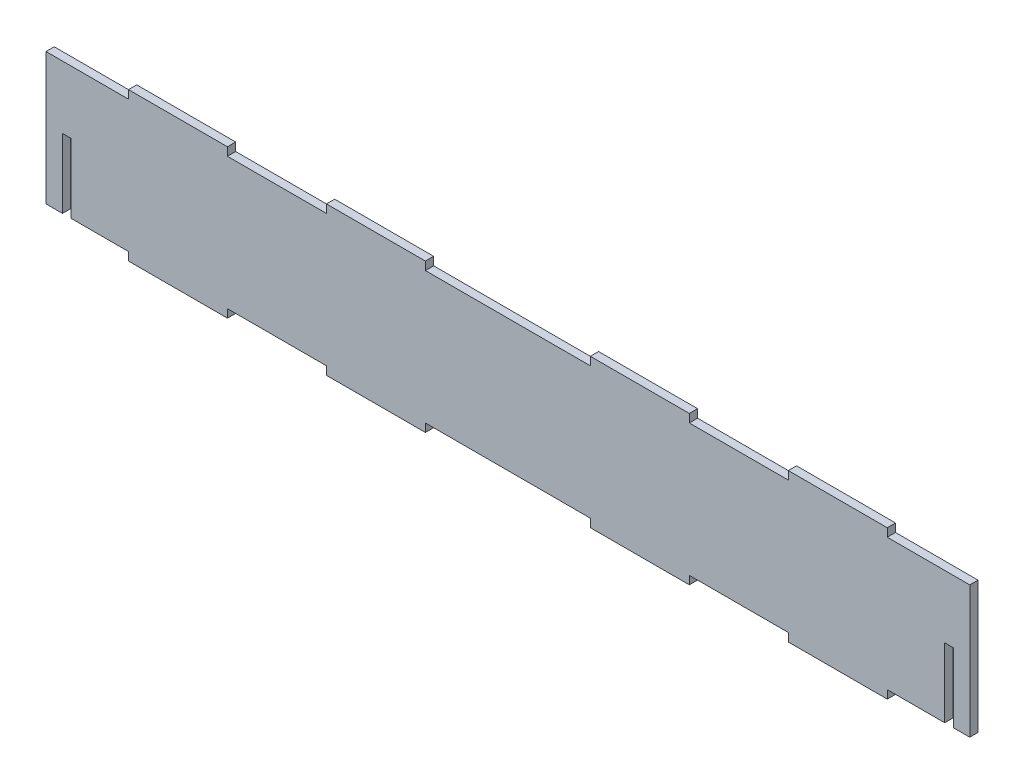
SolidWorks part; units mm, degrees
ref_plane "Front Plane" through (0, 0, 0) normal (0, 0, 1) x (1, 0, 0)
ref_plane "Top Plane" through (0, 0, 0) normal (0, 1, 0) x (1, 0, 0)
ref_plane "Right Plane" through (0, 0, 0) normal (1, 0, 0) x (0, 0, -1)
sketch "Sketch1" plane through (0, 0, 0) normal (0, 0, 1) x (1, 0, 0)
  line L1 (0, 50.8) -> (355.6, 50.8)
  line L2 (0, 50.8) -> (0, 0)
  line L3 (0, 0) -> (355.6, 0)
  line L4 (355.6, 50.8) -> (355.6, 0)
  dimension "D1" = 50.8
  dimension "D2" = 355.6
extrude "Boss-Extrude1" add sketch "Sketch1" along normal blind 3.175
ref_plane "Plane1" through (177.8, 0, 0) normal (-1, 0, 0) x (0, 0, 1)
ref_plane "Plane2" through (0, 25.4, 0) normal (0, 1, 0) x (1, 0, 0)
sketch "Sketch2" plane through (0, 50.8, 0) normal (0, 1, 0) x (1, 0, 0)
  line L0 (-55, 0) -> (55, 0) construction
  line L1 (31.75, 0) -> (69.85, 0)
  line L2 (31.75, 0) -> (31.75, -3.175)
  line L3 (31.75, -3.175) -> (69.85, -3.175)
  line L4 (69.85, 0) -> (69.85, -3.175)
  line L5 (355.6, 0) -> (0, 0) construction
  line L6 (107.95, 0) -> (146.05, 0)
  line L7 (107.95, 0) -> (107.95, -3.175)
  line L8 (107.95, -3.175) -> (146.05, -3.175)
  line L9 (146.05, 0) -> (146.05, -3.175)
  line L10 (355.6, -3.175) -> (0, -3.175) construction
  line L11 (50.8, -3.175) -> (50.8, 0) construction
  line L12 (127, -3.175) -> (127, 0) construction
  line L13 (177.8, 1.7463) -> (177.8, -1.7463) construction
  dimension "D1" = 76.2
  dimension "D2" = 50.8
  dimension "D3" = 38.1
extrude "Boss-Extrude2" add sketch "Sketch2" along normal blind 3.175
mirror "Mirror1" about plane through (177.8, 0, 0) normal (-1, 0, 0) of "Boss-Extrude2"
mirror "Mirror2" about plane through (0, 25.4, 0) normal (0, 1, 0) of "Mirror1", "Boss-Extrude2"
sketch "Sketch3" plane through (0, 0, 0) normal (0, 0, -1) x (-1, 0, 0)
  line L0 (0, 1.7463) -> (0, -1.7463) construction
  line L1 (-6.35, 0) -> (-9.652, 0)
  line L2 (-6.35, 0) -> (-6.35, 26.67)
  line L3 (-6.35, 26.67) -> (-9.652, 26.67)
  line L4 (-9.652, 0) -> (-9.652, 26.67)
  line L5 (1.7463, 0) -> (-1.7463, 0) construction
  point P6 (-8.001, 0)
  dimension "D1" = 3.302
  dimension "D2" = 6.35
  dimension "D3" = 26.67
extrude "Cut-Extrude1" cut sketch "Sketch3" against normal blind 3.175
mirror "Mirror3" about plane through (177.8, 0, 0) normal (-1, 0, 0) of "Cut-Extrude1"
equation "\"teeth\"= 1.5in'Teeth Width"
equation "\"D3@Sketch2\"=\"teeth\""
equation "\"t\"= 0.125'Sheet Thicness"
equation "\"teeth_tol\"= 0.001in'Tolerance betwee Teeth"
